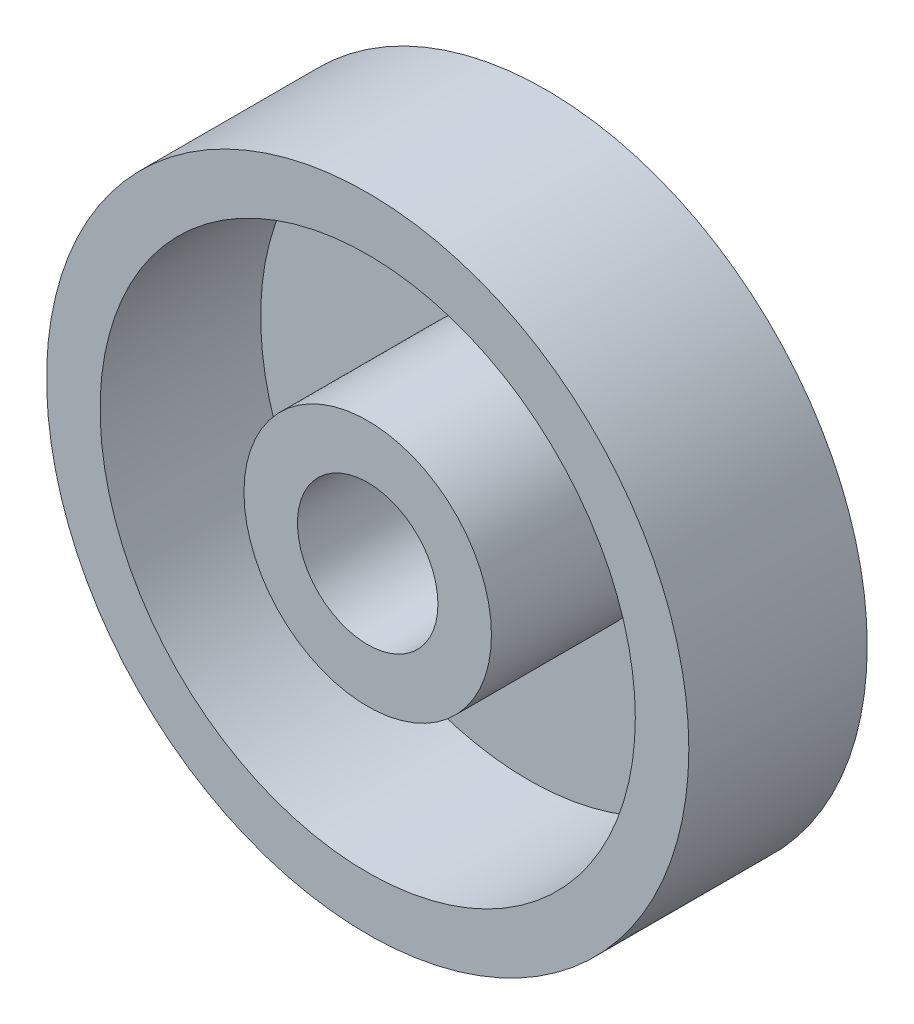
SolidWorks part; units mm, degrees
material "AISI 304"
ref_plane "Front Plane" through (0, 0, 0) normal (0, 0, 1) x (1, 0, 0)
ref_plane "Top Plane" through (0, 0, 0) normal (0, 1, 0) x (1, 0, 0)
ref_plane "Right Plane" through (0, 0, 0) normal (1, 0, 0) x (0, 0, -1)
sketch "Sketch2" plane through (0, 0, 0) normal (0, 0, 1) x (1, 0, 0)
  circle A0 centre (0, 0) radius 228.6
  circle A1 centre (0, 0) radius 50
extrude "Boss-Extrude1" add sketch "Sketch2" along normal blind 127
sketch "Sketch5" plane through (0, 0, 127) normal (0, 0, 1) x (1, 0, 0)
  circle A0 centre (0, 0) radius 190.5
  circle A1 centre (0, 0) radius 88.1
extrude "Cut-Extrude1" cut sketch "Sketch5" against normal blind 114.3
